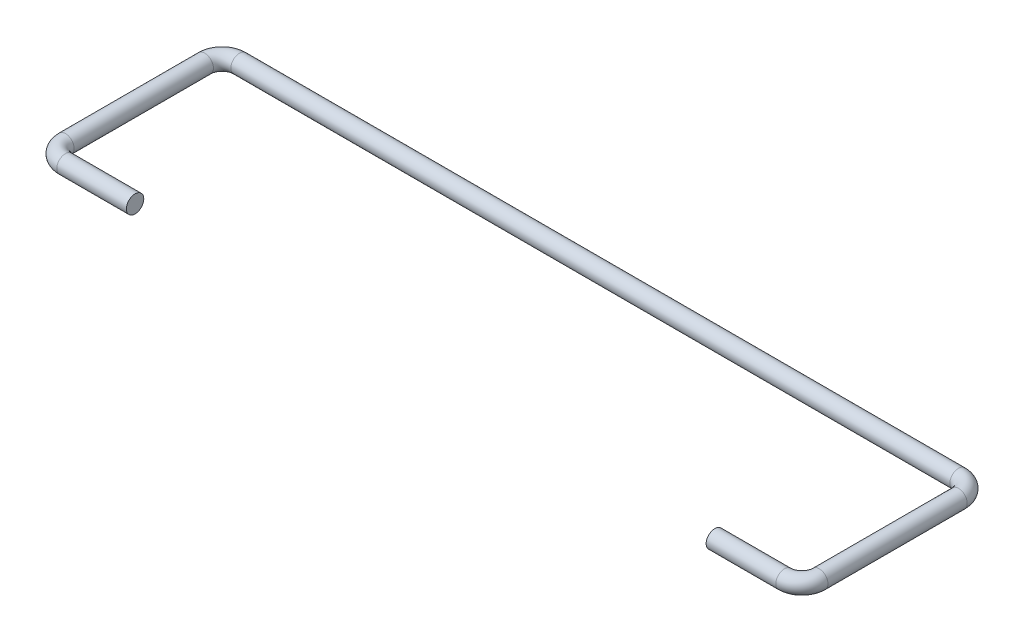
SolidWorks part; units mm, degrees
ref_plane "Front Plane" through (0, 0, 0) normal (0, 0, 1) x (1, 0, 0)
ref_plane "Top Plane" through (0, 0, 0) normal (0, 1, 0) x (1, 0, 0)
ref_plane "Right Plane" through (0, 0, 0) normal (1, 0, 0) x (0, 0, -1)
sketch "Sketch2" plane through (0, 0, 0) normal (0, 1, 0) x (1, 0, 0)
  line L0 (-55, 2.54) -> (-55, 22.86)
  line L1 (-52.46, 25.4) -> (52.46, 25.4)
  line L2 (55, 22.86) -> (55, 2.54)
  line L3 (-52.46, 0) -> (-42.3, 0)
  line L4 (52.46, 0) -> (42.3, 0)
  arc A0 (52.46, 25.4) -> (55, 22.86) centre (52.46, 22.86) cw
  arc A1 (-55, 22.86) -> (-52.46, 25.4) centre (-52.46, 22.86) cw
  arc A2 (55, 2.54) -> (52.46, 0) centre (52.46, 2.54) cw
  arc A3 (-55, 2.54) -> (-52.46, 0) centre (-52.46, 2.54) ccw
  point P13 (55, 0)
  point P16 (-55, 0)
  point P17 (0, 25.4)
  dimension "D1" = 2.54
  dimension "D4" = 2.54
  dimension "D2" = 110
  dimension "D3" = 12.7
  dimension "D5" = 25.4
ref_plane "Plane1" through (-42.3, 0, 0) normal (1, 0, 0) x (0, 0, -1)
sketch "Sketch4" plane through (-42.3, 0, 0) normal (1, 0, 0) x (0, 0, -1)
  circle A0 centre (0, 0) radius 1.27
  dimension "D1" = 2.54
sweep "Sweep3" add profiles "Sketch4" path "Sketch2"
